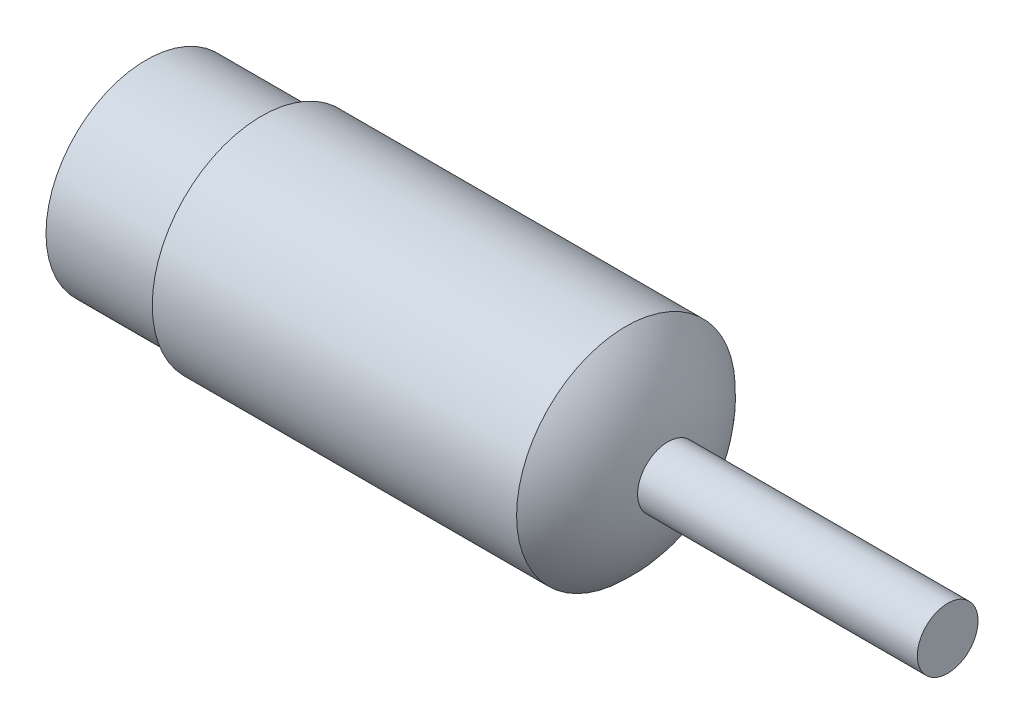
SolidWorks part; units mm, degrees
material "普通碳钢"
ref_plane "前视基准面" through (0, 0, 0) normal (0, 0, 1) x (1, 0, 0)
ref_plane "上视基准面" through (0, 0, 0) normal (0, 1, 0) x (1, 0, 0)
ref_plane "右视基准面" through (0, 0, 0) normal (1, 0, 0) x (0, 0, -1)
sketch "Sketch1" plane through (0, 0, 0) normal (0, 0, 1) x (1, 0, 0)
  line L0 (0, 0) -> (61.0223, 0) construction
  line L1 (0, 0) -> (0, 8.25)
  line L2 (0, 8.25) -> (9.5, 8.25)
  line L3 (9.5, 8.25) -> (9.5, 9)
  line L4 (9.5, 9) -> (39.5, 9)
  line L5 (43, 0) -> (0, 0)
  arc A0 (39.5, 9) -> (43, 0) centre (32.4915, 1.0939) cw
  dimension "D1" = 16.5
  dimension "D2" = 9.5
  dimension "D3" = 30
  dimension "D4" = 18
  dimension "D5" = 43
revolve "Revolve1" add sketch "Sketch1" angle 360 about L0
sketch "Sketch2" plane through (0, 0, 0) normal (-1, 0, 0) x (0, 0, 1)
  circle A0 centre (0, 0) radius 2.5
  dimension "D1" = 5
extrude "Boss-Extrude1" add sketch "Sketch2" against normal blind 66
